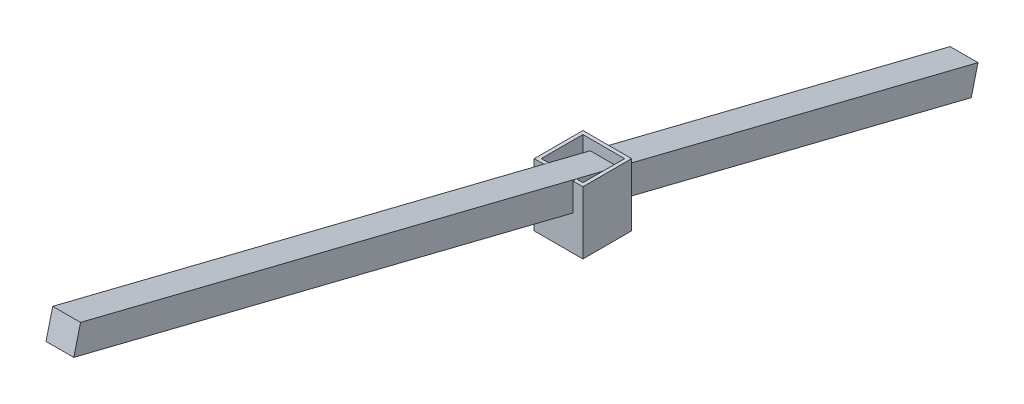
SolidWorks part; units mm, degrees
ref_plane "Front" through (0, 0, 0) normal (0, 0, 1) x (1, 0, 0)
ref_plane "Top" through (0, 0, 0) normal (0, 1, 0) x (1, 0, 0)
ref_plane "Right" through (0, 0, 0) normal (1, 0, 0) x (0, 0, -1)
sketch "Sketch1" plane through (0, 0, 0) normal (0, 1, 0) x (1, 0, 0)
  line L0 (0, 0) -> (17.5, 0) construction
  line L1 (-17.5, 17.5) -> (0, 0) construction
  line L2 (-15, 15) -> (-15, -15)
  line L3 (-15, -15) -> (15, -15)
  line L4 (15, 15) -> (15, -15)
  line L5 (0, 0) -> (15, -15) construction
  line L6 (-15, -15) -> (0, 0) construction
  line L7 (0, 0) -> (17.5, 17.5) construction
  line L8 (-17.5, 17.5) -> (-17.5, -17.5)
  line L9 (-17.5, -17.5) -> (17.5, -17.5)
  line L10 (17.5, 17.5) -> (17.5, -17.5)
  line L11 (0, 0) -> (17.5, -17.5) construction
  line L12 (-17.5, -17.5) -> (0, 0) construction
  line L13 (-15, 15) -> (0, 0) construction
  line L14 (0, 0) -> (15, 15) construction
  line L15 (-17.5, 17.5) -> (17.5, 17.5)
  line L16 (-15, 15) -> (15, 15)
  point P0 (0, 0)
  point P6 (0, 0)
  point P12 (-15, 0)
  point P14 (15, 0)
  point P16 (-17.5, 0)
  dimension "D2" = 30
  dimension "D4" = 35
extrude "Boss-Extrude1" add sketch "Sketch1" against normal blind 45
sketch3d "Angled Plane" plane through (0, 0, 0) normal (0, 0, 1) x (1, 0, 0)
  dimension "D1" = 14
sketch "Sketch5" plane through (0, 4.6947, 18.8295) normal (0, -0.2419, -0.9703) x (1, 0, 0)
  line L0 (-15, 3.6288) -> (15, 3.6288) construction
  line L1 (10.25, 3.6288) -> (-9.75, 3.6288)
  line L2 (10.25, 3.6288) -> (10.25, 23.6288)
  line L3 (10.25, 23.6288) -> (-9.75, 23.6288)
  line L4 (-9.75, 3.6288) -> (-9.75, 23.6288)
  line L5 (17.5, 4.2336) -> (17.5, -4.2336) construction
  dimension "D1" = 20
  dimension "D2" = 20
  dimension "D3" = 7.25
extrude "Boss-Extrude3" add sketch "Sketch5" along normal blind 302.5 and the other way blind 362.5
sketch3d "3DSketch10"
  line L1 (15, 0, -15) -> (-15, 0, -15) construction
  line L2 (-10.25, 0, -15) -> (9.75, 0, -15)
  line L3 (-10.25, 0, -15) -> (-10.25, -19.4059, -10.1616)
  line L4 (-10.25, -19.4059, -10.1616) -> (9.75, -19.4059, -10.1616)
  line L5 (9.75, 0, -15) -> (9.75, -19.4059, -10.1616)
  dimension "D1" = 166
  dimension "D2" = 20
  dimension "D3" = 20
  dimension "D4" = 7.25
